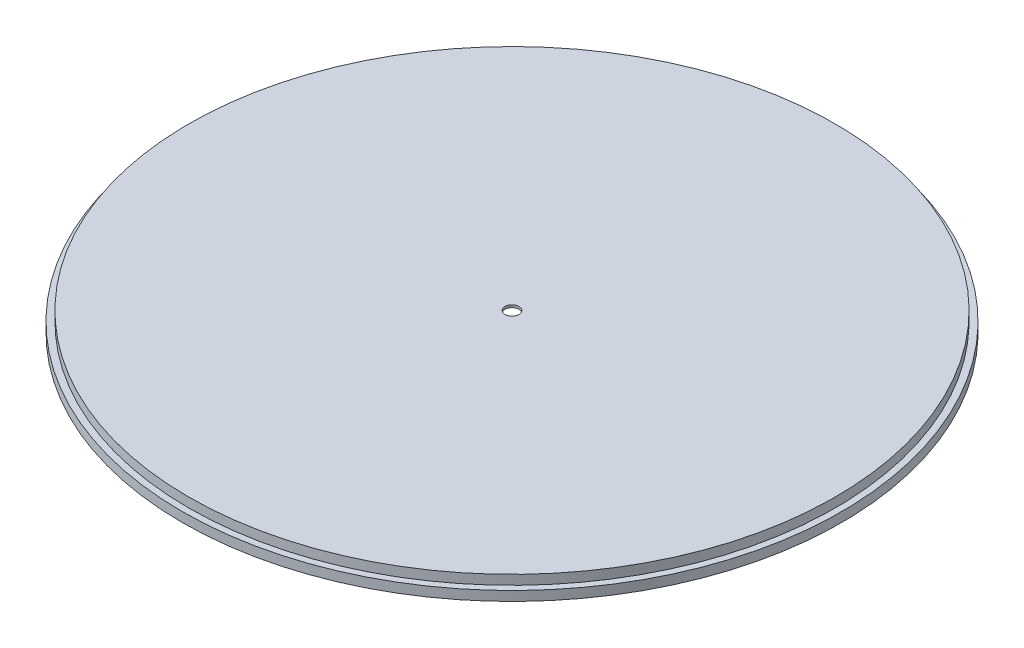
SolidWorks part; units mm, degrees
ref_plane "Front Plane" through (0, 0, 0) normal (0, 0, 1) x (1, 0, 0)
ref_plane "Top Plane" through (0, 0, 0) normal (0, 1, 0) x (1, 0, 0)
ref_plane "Right Plane" through (0, 0, 0) normal (1, 0, 0) x (0, 0, -1)
sketch "Sketch1" plane through (0, 0, 0) normal (0, 1, 0) x (1, 0, 0)
  circle A0 centre (0, 0) radius 25.5
  dimension "D1" = 51
extrude "Boss-Extrude1" add sketch "Sketch1" against normal blind 1.5
sketch "Sketch2" plane through (0, -1.5, 0) normal (0, -1, 0) x (-1, 0, 0)
  circle A0 centre (0, 0) radius 26
  circle A1 centre (0, 0) radius 25.5
  circle A2 centre (0, 0) radius 25.5
  dimension "D1" = 0
  dimension "D2" = 0.5
extrude "Boss-Extrude2" add sketch "Sketch2" against normal blind 0.75 contours A0
sketch "Sketch3" plane through (0, -0.75, 0) normal (0, 1, 0) x (1, 0, 0)
  circle A0 centre (0, 0) radius 0.6
  dimension "D1" = 1.2
extrude "Cut-Extrude1" cut sketch "Sketch3" against normal through all
sketch "Sketch4" plane through (0, 0, 0) normal (0, 0, 1) x (1, 0, 0)
  line L8 (-4.35, -1.5) -> (0, -1.5)
  line L9 (-4.35, -1.5) -> (-0.55, -0.2)
  line L11 (-0.55, -0.2) -> (-0.55, 0)
  line L12 (-0.55, 0) -> (0, 0)
  line L13 (0, -1.5) -> (0, 0)
  line L15 (0, -0.75) -> (0, -1.5) construction
  line L16 (-26, -1.5) -> (26, -1.5) construction
  dimension "D1" = 4.35
  dimension "D2" = 0.55
  dimension "D4" = 0.2
revolve "Cut-Revolve1" cut sketch "Sketch4" angle 360 about L13
